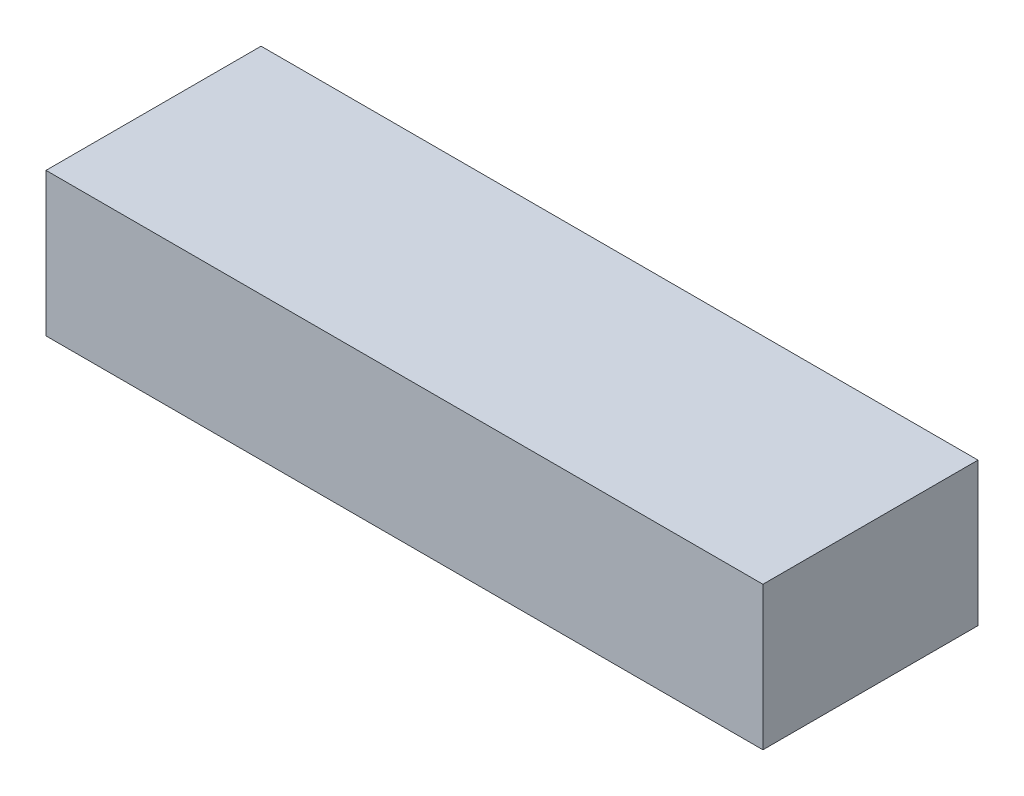
SolidWorks part; units mm, degrees
ref_plane "Front Plane" through (0, 0, 0) normal (0, 0, 1) x (1, 0, 0)
ref_plane "Top Plane" through (0, 0, 0) normal (0, 1, 0) x (1, 0, 0)
ref_plane "Right Plane" through (0, 0, 0) normal (1, 0, 0) x (0, 0, -1)
sketch "Sketch1" plane through (0, 0, 0) normal (0, 1, 0) x (1, 0, 0)
  line L0 (0, -19.05) -> (0, 0) construction
  line L1 (-63.5, 19.05) -> (63.5, 19.05)
  line L2 (-63.5, 19.05) -> (-63.5, -19.05)
  line L3 (-63.5, -19.05) -> (63.5, -19.05)
  line L4 (63.5, 19.05) -> (63.5, -19.05)
  line L5 (0, 0) -> (63.5, 0) construction
  dimension "D1" = 38.1
  dimension "D2" = 127
extrude "Extrude1" add sketch "Sketch1" along normal blind 25.4
